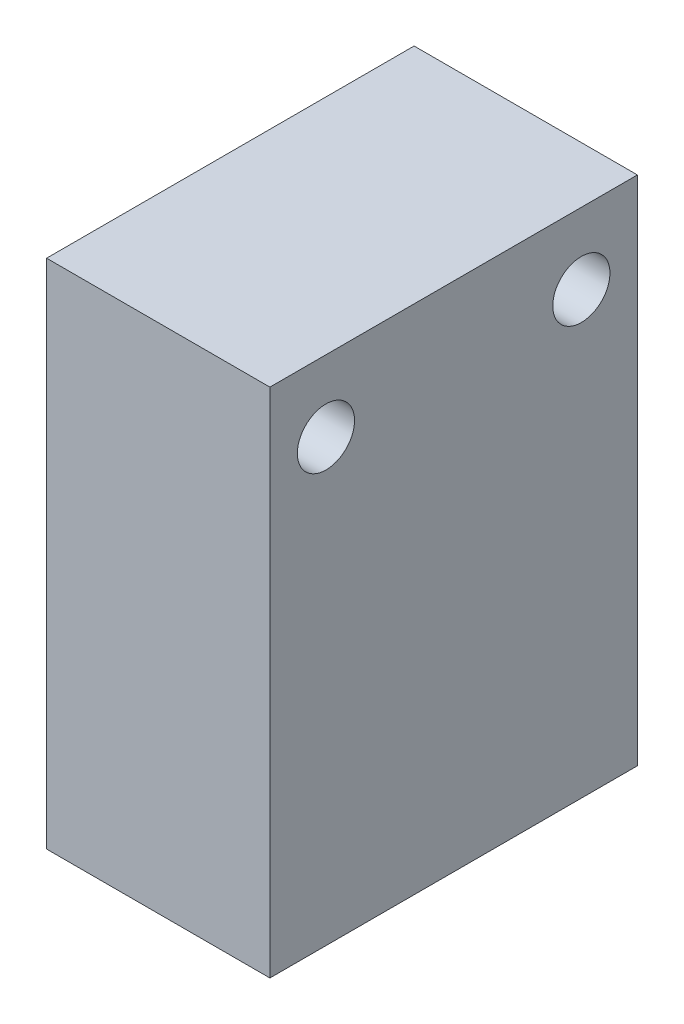
SolidWorks part; units mm, degrees
ref_plane "Front Plane" through (0, 0, 0) normal (0, 0, 1) x (1, 0, 0)
ref_plane "Top Plane" through (0, 0, 0) normal (0, 1, 0) x (1, 0, 0)
ref_plane "Right Plane" through (0, 0, 0) normal (1, 0, 0) x (0, 0, -1)
sketch "Sketch1" plane through (0, 0, 0) normal (0, 1, 0) x (1, 0, 0)
  line L1 (-6.096, -10.033) -> (6.096, -10.033)
  line L2 (-6.096, -10.033) -> (-6.096, 10.033)
  line L3 (-6.096, 10.033) -> (6.096, 10.033)
  line L4 (6.096, -10.033) -> (6.096, 10.033)
  line L5 (-6.096, -10.033) -> (6.096, 10.033) construction
  line L6 (-6.096, 10.033) -> (6.096, -10.033) construction
  point P0 (0, 0)
  dimension "D1" = 12.192
  dimension "D2" = 20.066
extrude "Boss-Extrude1" add sketch "Sketch1" along normal blind 27.94
sketch "Sketch3" plane through (-6.096, 0, 0) normal (-1, 0, 0) x (0, 0, 1)
  line L0 (0, 0) -> (0, 14.8043) construction
  line L1 (-6.9723, 24.0538) -> (10.033, 24.0538) construction
  line L3 (-10.033, 27.94) -> (10.033, 27.94) construction
  circle A0 centre (-6.9723, 24.0538) radius 1.5621
  circle A1 centre (6.9723, 24.0538) radius 1.5621
  dimension "D4" = 3.1242
  dimension "D1" = 3.8862
  dimension "D2" = 6.9723
  dimension "D3" = 6.9723
extrude "Cut-Extrude1" cut sketch "Sketch3" against normal through all both and the other way through all
